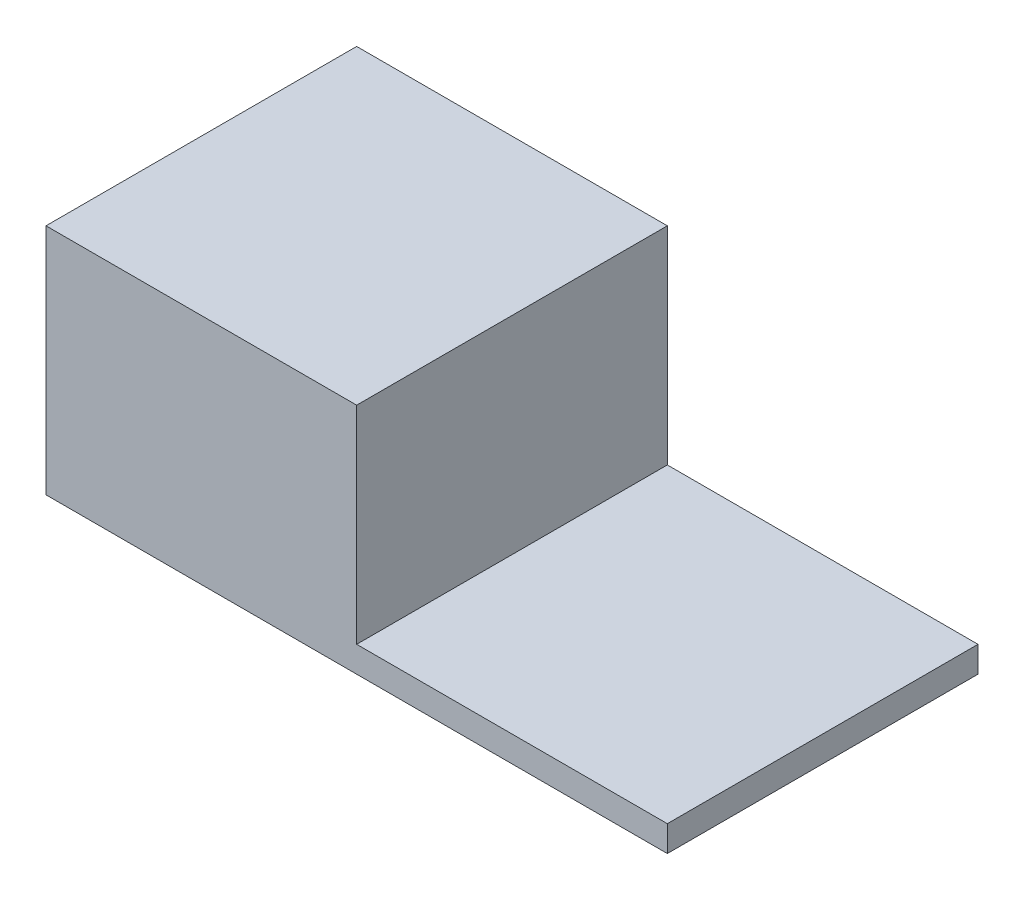
SolidWorks part; units mm, degrees
ref_plane "正面" through (0, 0, 0) normal (0, 0, 1) x (1, 0, 0)
ref_plane "平面" through (0, 0, 0) normal (0, 1, 0) x (1, 0, 0)
ref_plane "右側面" through (0, 0, 0) normal (1, 0, 0) x (0, 0, -1)
sketch "ｽｹｯﾁ1" plane through (0, 0, 0) normal (0, 0, 1) x (1, 0, 0)
  line L1 (0, 0) -> (1200, 0)
  line L2 (0, 0) -> (0, 50)
  line L3 (0, 50) -> (1200, 50)
  line L4 (1200, 0) -> (1200, 50)
  line L5 (0, 50) -> (600, 50)
  line L6 (0, 50) -> (0, 450)
  line L7 (0, 450) -> (600, 450)
  line L8 (600, 50) -> (600, 450)
  dimension "D1" = 50
  dimension "D2" = 400
  dimension "D3" = 600
  dimension "D4" = 1200
extrude "ﾎﾞｽ - 押し出し1" add sketch "ｽｹｯﾁ1" along normal blind 600 contours L1 L4 L3 L2 | L3 L8 L7 L6
